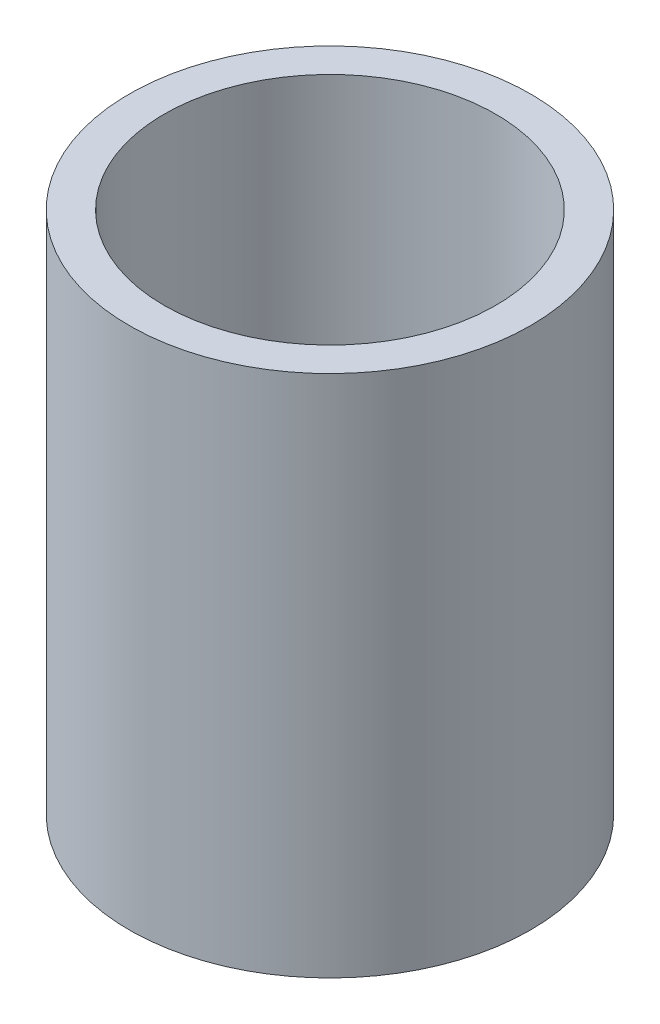
SolidWorks part; units mm, degrees
ref_plane "Спереди" through (0, 0, 0) normal (0, 0, 1) x (1, 0, 0)
ref_plane "Сверху" through (0, 0, 0) normal (0, 1, 0) x (1, 0, 0)
ref_plane "Справа" through (0, 0, 0) normal (1, 0, 0) x (0, 0, -1)
sketch "Эскиз1" plane through (0, 0, 0) normal (0, 1, 0) x (1, 0, 0)
  circle A0 centre (0, 0) radius 47.5
extrude "Вытянуть-Тонкостенный1" add sketch "Эскиз1" along normal blind 150 thin
